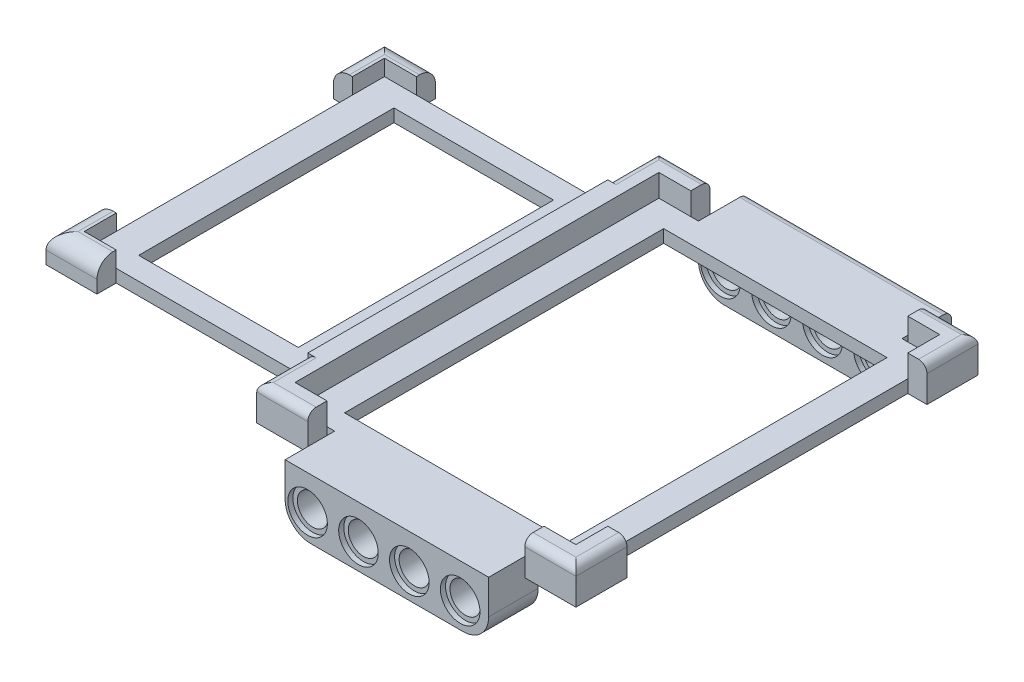
SolidWorks part; units mm, degrees
ref_plane "Front Plane" through (0, 0, 0) normal (0, 0, 1) x (1, 0, 0)
ref_plane "Top Plane" through (0, 0, 0) normal (0, 1, 0) x (1, 0, 0)
ref_plane "Right Plane" through (0, 0, 0) normal (1, 0, 0) x (0, 0, -1)
sketch "Sketch1" plane through (0, 0, 0) normal (0, 1, 0) x (1, 0, 0)
  line L1 (0, 0) -> (44, 0)
  line L2 (0, 0) -> (0, 57)
  line L3 (0, 57) -> (44, 57)
  line L4 (44, 0) -> (44, 57)
  dimension "D1" = 44
  dimension "D2" = 57
extrude "Boss-Extrude1" add sketch "Sketch1" along normal blind 2
sketch "Sketch2" plane through (0, 2, 0) normal (0, 1, 0) x (1, 0, 0)
  line L0 (22, 0) -> (22, 57) construction
  line L2 (0, 0) -> (0, 5)
  line L3 (0, 5) -> (-3, 5)
  line L4 (-3, 0) -> (-3, 5)
  line L5 (0, 0) -> (5, 0)
  line L6 (-3, 0) -> (-3, -3)
  line L7 (-3, -3) -> (5, -3)
  line L8 (5, 0) -> (5, -3)
  line L9 (0, 0) -> (44, 0) construction
  line L10 (44, 57) -> (0, 57) construction
  line L11 (47, 0) -> (47, -3)
  line L12 (47, -3) -> (39, -3)
  line L13 (39, 0) -> (39, -3)
  line L14 (44, 0) -> (39, 0)
  line L15 (44, 0) -> (44, 5)
  line L16 (44, 5) -> (47, 5)
  line L17 (47, 0) -> (47, 5)
  line L18 (0, 28.5) -> (44, 28.5) construction
  line L19 (0, 57) -> (0, 0) construction
  line L20 (44, 0) -> (44, 57) construction
  line L21 (47, 57) -> (47, 52)
  line L22 (44, 52) -> (47, 52)
  line L23 (44, 57) -> (44, 52)
  line L24 (44, 57) -> (39, 57)
  line L25 (39, 57) -> (39, 60)
  line L26 (47, 60) -> (39, 60)
  line L27 (47, 57) -> (47, 60)
  line L28 (-3, 57) -> (-3, 60)
  line L29 (-3, 60) -> (5, 60)
  line L30 (5, 57) -> (5, 60)
  line L31 (0, 57) -> (5, 57)
  line L32 (0, 57) -> (0, 52)
  line L33 (0, 52) -> (-3, 52)
  line L34 (-3, 57) -> (-3, 52)
  dimension "D1" = 5
  dimension "D2" = 3
  dimension "D3" = 8
  dimension "D4" = 3
  dimension "D5" = 5
extrude "Boss-Extrude2" add sketch "Sketch2" against normal blind 2 and the other way blind 3.5
sketch "Sketch8" plane through (0, 2, 0) normal (0, 1, 0) x (1, 0, 0)
  line L0 (39, 57) -> (5, 57) construction
  line L1 (38.0957, 57) -> (6.2057, 57)
  line L2 (38.0957, 57) -> (38.0957, 64.76)
  line L3 (38.0957, 64.76) -> (6.2057, 64.76)
  line L4 (6.2057, 57) -> (6.2057, 64.76)
  line L5 (44, 28.5) -> (-1.5501, 28.5) construction
  line L6 (44, 5) -> (44, 52) construction
  line L7 (38.0957, -7.76) -> (6.2057, -7.76)
  line L8 (6.2057, 0) -> (6.2057, -7.76)
  line L9 (38.0957, 0) -> (6.2057, 0)
  line L10 (38.0957, 0) -> (38.0957, -7.76)
  dimension "D1" = 31.89
  dimension "D2" = 7.76
sketch "Sketch17" plane through (0, 0, 0) normal (-1, 0, 0) x (0, 0, 1)
  line L1 (-52, 2) -> (-4.9751, 2)
  line L2 (-52, 2) -> (-52, 0)
  line L3 (-52, 0) -> (-4.9751, 0)
  line L4 (-4.9751, 2) -> (-4.9751, 0)
  dimension "D1" = 47.0249
extrude "Boss-Extrude7" add sketch "Sketch17" along normal blind 38
extrude "Boss-Extrude5" add sketch "Sketch8" against normal blind 9.38
sketch "Sketch9" plane through (0, 0, -64.76) normal (0, 0, -1) x (-1, 0, 0)
  circle A0 centre (-33.6338, -3.3837) radius 2.4
  circle A1 centre (-25.6638, -3.3837) radius 2.4
  circle A2 centre (-17.6938, -3.3837) radius 2.4
  circle A3 centre (-9.7238, -3.3837) radius 2.4
  dimension "D1" = 4.8
  dimension "D2" = 4
extrude "Cut-Extrude1" cut sketch "Sketch9" against normal blind 9.38
sketch "Sketch10" plane through (0, 0, -64.76) normal (0, 0, -1) x (-1, 0, 0)
  circle A0 centre (-33.6338, -3.3837) radius 3.1
  circle A1 centre (-33.6338, -3.3837) radius 2.4 construction
  circle A2 centre (-25.6638, -3.3837) radius 3.1
  circle A3 centre (-17.6938, -3.3837) radius 3.1
  circle A4 centre (-9.7238, -3.3837) radius 3.1
  dimension "D2" = 6.2
  dimension "D1" = 0
  dimension "D3" = 4
extrude "Cut-Extrude2" cut sketch "Sketch10" against normal blind 0.8
sketch "Sketch11" plane through (0, 0, -57) normal (0, 0, 1) x (1, 0, 0)
  circle A0 centre (33.6338, -3.3837) radius 3.1
  circle A1 centre (33.6338, -3.3837) radius 2.4 construction
  circle A2 centre (25.6338, -3.3837) radius 3.1
  circle A3 centre (17.6338, -3.3837) radius 3.1
  circle A4 centre (9.6338, -3.3837) radius 3.1
  point P4 (57.6338, -3.3837)
  dimension "D1" = 0
  dimension "D2" = 6.2
  dimension "D3" = 4
extrude "Cut-Extrude3" cut sketch "Sketch11" against normal blind 0.8
sketch "Sketch14" plane through (0, 0, 7.76) normal (0, 0, 1) x (1, 0, 0)
  circle A0 centre (9.7238, -3.3837) radius 2.4
  circle A1 centre (9.7238, -3.3837) radius 2.4 construction
  circle A2 centre (17.6938, -3.3837) radius 2.4
  circle A3 centre (25.6638, -3.3837) radius 2.4
  circle A4 centre (33.6338, -3.3837) radius 2.4
  dimension "D1" = 0
  dimension "D3" = 4.8
  dimension "D2" = 4
extrude "Cut-Extrude5" cut sketch "Sketch14" against normal blind 77.6
sketch "Sketch15" plane through (0, 0, 7.76) normal (0, 0, 1) x (1, 0, 0)
  circle A0 centre (9.7238, -3.3837) radius 3.1
  circle A1 centre (9.7238, -3.3837) radius 2.4 construction
  circle A2 centre (17.6938, -3.3837) radius 3.1
  circle A3 centre (25.6638, -3.3837) radius 3.1
  circle A4 centre (33.6338, -3.3837) radius 3.1
  dimension "D1" = 6.2
  dimension "D2" = 0
  dimension "D3" = 4
extrude "Cut-Extrude6" cut sketch "Sketch15" against normal blind 0.8
sketch "Sketch16" plane through (0, 0, 0) normal (0, 0, -1) x (-1, 0, 0)
  circle A0 centre (-9.7238, -3.3837) radius 3.1
  circle A1 centre (-9.7238, -3.3837) radius 2.4 construction
  circle A2 centre (-17.6938, -3.3837) radius 3.1
  circle A3 centre (-25.6638, -3.3837) radius 3.1
  circle A4 centre (-33.6338, -3.3837) radius 3.1
  dimension "D1" = 6.2
  dimension "D2" = 0
  dimension "D3" = 4
extrude "Cut-Extrude7" cut sketch "Sketch16" against normal blind 0.8
fillet "Fillet1" radius 1.3 2 edges at (47, 5.5, -56) (43, 5.5, -60)
fillet "Fillet2" radius 1.3 2 edges at (47, 5.5, -1) (43, 5.5, 3)
fillet "Fillet3" radius 1.3 2 edges at (-3, 5.5, -56) (1, 5.5, -60)
fillet "Fillet4" radius 1.3 2 edges at (-3, 5.5, -1) (1, 5.5, 3)
fillet "Fillet5" radius 1.3 1 edges at (22.1507, 2, -64.76)
fillet "Fillet7" radius 4 1 edges at (6.2057, -7.38, -60.88)
fillet "Fillet8" radius 4 1 edges at (38.0957, -7.38, -60.88)
fillet "Fillet9" radius 4 1 edges at (38.0957, -7.38, 3.88)
fillet "Fillet10" radius 4 1 edges at (6.2057, -7.38, 3.88)
sketch "Sketch19" plane through (0, 2, 0) normal (0, 1, 0) x (1, 0, 0)
  line L1 (-3, 52) -> (0, 52)
  line L2 (-3, 52) -> (-3, 5)
  line L3 (-3, 5) -> (0, 5)
  line L4 (0, 52) -> (0, 5)
  dimension "D1" = 3
extrude "Boss-Extrude9" add sketch "Sketch19" along normal blind 3.5
sketch "Sketch20" plane through (0, 2, 0) normal (0, 1, 0) x (1, 0, 0)
  line L0 (-38, 4.9751) -> (-38, 52) construction
  line L1 (-33, 48.5) -> (-8, 48.5)
  line L2 (-33, 48.5) -> (-33, 8.5)
  line L3 (-33, 8.5) -> (-8, 8.5)
  line L4 (-8, 48.5) -> (-8, 8.5)
  line L5 (-38, 52) -> (-3, 52) construction
  dimension "D1" = 25
  dimension "D2" = 40
  dimension "D3" = 5
  dimension "D4" = 3.5
extrude "Cut-Extrude8" cut sketch "Sketch20" against normal through all
sketch "Sketch21" plane through (0, 2, 0) normal (0, 1, 0) x (1, 0, 0)
  line L0 (44, 5) -> (44, 52) construction
  line L1 (4.5, 53.25) -> (39.5, 53.25)
  line L2 (4.5, 53.25) -> (4.5, 3.25)
  line L3 (4.5, 3.25) -> (39.5, 3.25)
  line L4 (39.5, 53.25) -> (39.5, 3.25)
  line L5 (6.2057, 57) -> (5, 57) construction
  dimension "D1" = 35
  dimension "D2" = 50
  dimension "D3" = 4.5
  dimension "D4" = 3.75
extrude "Cut-Extrude9" cut sketch "Sketch21" against normal blind 3.5
sketch "Sketch22" plane through (0, 2, 0) normal (0, 1, 0) x (1, 0, 0)
  line L0 (-38, 52) -> (-32.9999, 52)
  line L1 (-38, 52) -> (-3, 52) construction
  line L2 (-32.9999, 52) -> (-32.9999, 55.0051)
  line L3 (-32.9999, 55.0051) -> (-38, 55.0051)
  line L5 (-38, 52) -> (-38, 46.982)
  line L6 (-38, 4.9751) -> (-38, 52) construction
  line L7 (-38, 46.982) -> (-40.9883, 46.982)
  line L8 (-40.9883, 46.982) -> (-40.9883, 55.0051)
  line L9 (-40.9883, 55.0051) -> (-38, 55.0051)
  line L10 (-38, 28.4876) -> (-3, 28.4876) construction
  line L11 (-3, 4.9751) -> (-3, 52) construction
  line L12 (-32.9999, 4.9751) -> (-32.9999, 1.97)
  line L13 (-38, 4.9751) -> (-32.9999, 4.9751)
  line L14 (-38, 4.9751) -> (-38, 9.9931)
  line L15 (-38, 9.9931) -> (-40.9883, 9.9931)
  line L16 (-40.9883, 9.9931) -> (-40.9883, 1.97)
  line L17 (-40.9883, 1.97) -> (-38, 1.97)
  line L18 (-32.9999, 1.97) -> (-38, 1.97)
extrude "Boss-Extrude10" add sketch "Sketch22" along normal blind 2.5 and the other way blind 2
fillet "Fillet11" radius 2.5 2 edges at (-36.9941, 4.5, -55.0051) (-40.9883, 4.5, -50.9935)
fillet "Fillet12" radius 2.5 2 edges at (-40.9883, 4.5, -5.9816) (-36.9941, 4.5, -1.97)
